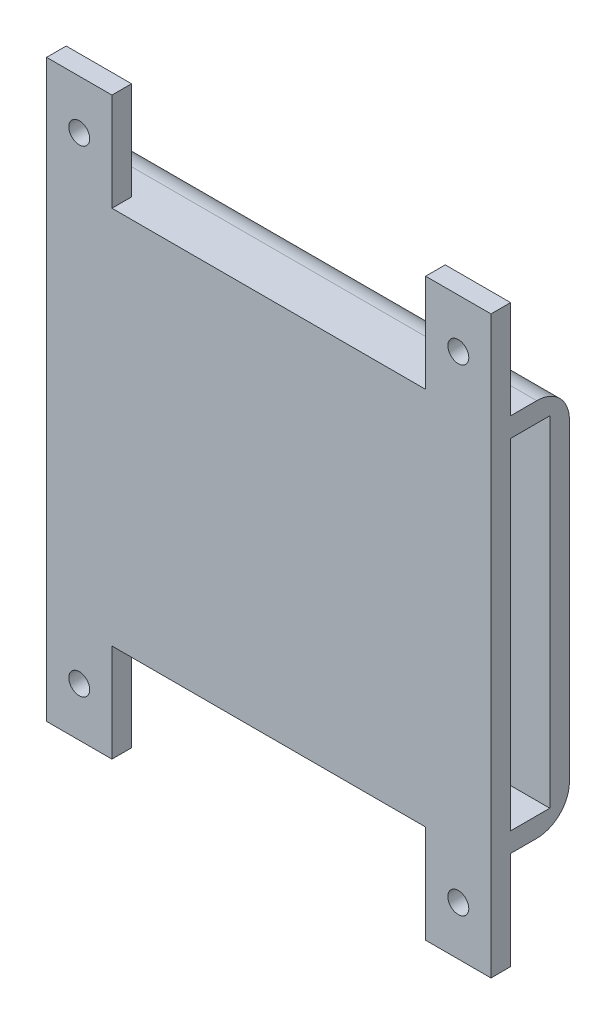
SolidWorks part; units mm, degrees
ref_plane "Plan de face" through (0, 0, 0) normal (0, 0, 1) x (1, 0, 0)
ref_plane "Plan de dessus" through (0, 0, 0) normal (0, 1, 0) x (1, 0, 0)
ref_plane "Plan de droite" through (0, 0, 0) normal (1, 0, 0) x (0, 0, -1)
sketch "Esquisse1" plane through (0, 0, 0) normal (0, 0, 1) x (1, 0, 0)
  line L1 (-34, 29) -> (34, 29)
  line L2 (-34, 29) -> (-34, -29)
  line L3 (-34, -29) -> (34, -29)
  line L4 (34, 29) -> (34, -29)
  line L5 (-34, 29) -> (34, -29) construction
  line L6 (-34, -29) -> (34, 29) construction
  point P0 (0, 0)
  dimension "D1" = 68
  dimension "D2" = 58
extrude "Boss.-Extru.1" add sketch "Esquisse1" along normal blind 3
sketch "Esquisse2" plane through (0, 0, 3) normal (0, 0, 1) x (1, 0, 0)
  line L9 (34, 26) -> (34, 29)
  line L10 (34, -29) -> (34, 29) construction
  line L11 (34, 29) -> (-34, 29)
  line L12 (-34, 29) -> (-34, -29)
  line L13 (-34, -29) -> (34, -29)
  line L14 (34, -29) -> (34, -26)
  line L15 (34, -26) -> (-31, -26)
  line L16 (-31, -26) -> (-31, 26)
  line L17 (-31, 26) -> (34, 26)
  dimension "D1" = 3
  dimension "D2" = 3
  dimension "D3" = 3
extrude "Boss.-Extru.2" add sketch "Esquisse2" along normal blind 9
sketch "Esquisse4" plane through (-31, 0, 0) normal (1, 0, 0) x (0, 0, -1)
  line L0 (-12, -26) -> (-3, -26) construction
  line L1 (-12, 26) -> (-9, 26)
  line L2 (-12, 26) -> (-12, -26)
  line L3 (-12, -26) -> (-9, -26)
  line L4 (-9, 26) -> (-9, -26)
  dimension "D1" = 3
extrude "Boss.-Extru.3" add sketch "Esquisse4" along normal blind 65
sketch "Esquisse6" plane through (0, -29, 0) normal (0, -1, 0) x (1, 0, 0)
  line L0 (0, 12) -> (0, 0) construction
  line L1 (-34, 12) -> (-24, 12)
  line L2 (-34, 12) -> (-34, 9)
  line L3 (-34, 9) -> (-24, 9)
  line L4 (-24, 12) -> (-24, 9)
  line L5 (-34, 12) -> (34, 12) construction
  line L6 (24, 12) -> (24, 9)
  line L7 (34, 9) -> (24, 9)
  line L8 (34, 12) -> (34, 9)
  line L9 (34, 12) -> (24, 12)
  dimension "D1" = 3
  dimension "D2" = 10
extrude "Boss.-Extru.4" add sketch "Esquisse6" along normal blind 15
sketch "Esquisse7" plane through (0, 0, 12) normal (0, 0, 1) x (1, 0, 0)
  line L0 (-24, -29) -> (-34, -29) construction
  line L1 (-29, -29) -> (-29, -44) construction
  line L2 (-24, -44) -> (-34, -44) construction
  line L3 (0, -29) -> (0, -44) construction
  line L4 (-24, -29) -> (24, -29) construction
  circle A0 centre (-29, -36.5) radius 1.6
  circle A1 centre (29, -36.5) radius 1.6
  dimension "D1" = 3.2
extrude "Enlèv. mat.-Extru.1" cut sketch "Esquisse7" against normal blind 3
mirror "Symétrie1" about plane through (0, 0, 0) normal (0, 1, 0) of "Boss.-Extru.4", "Enlèv. mat.-Extru.1"
fillet "Congé1" radius 5 3 edges at (0, -29, 0) (0, 29, 0) (-34, 0, 0)
